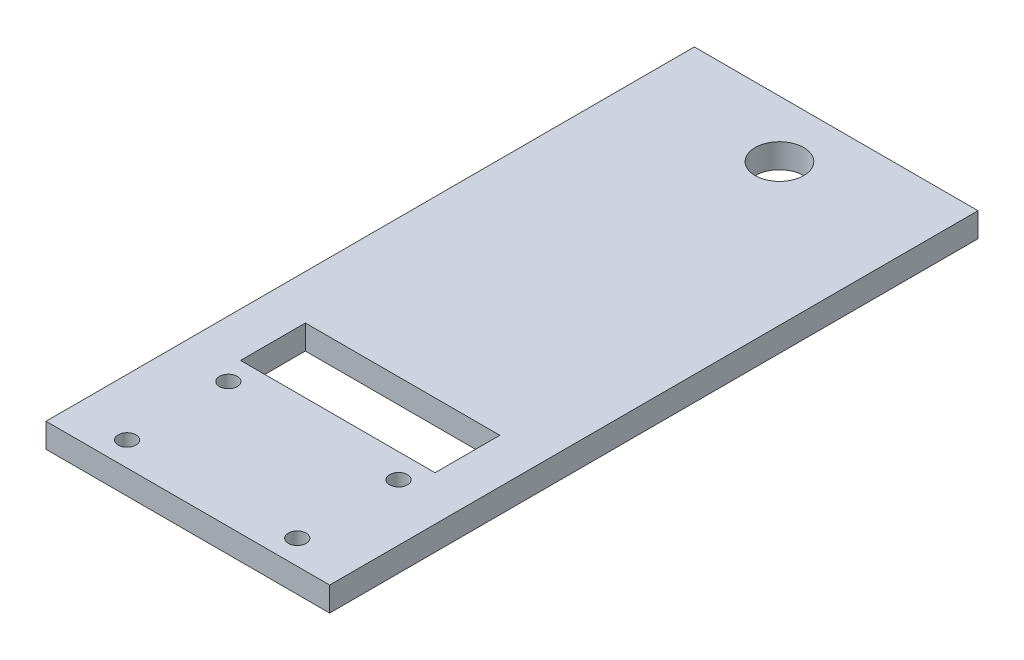
SolidWorks part; units mm, degrees
ref_plane "Front Plane" through (0, 0, 0) normal (0, 0, 1) x (1, 0, 0)
ref_plane "Top Plane" through (0, 0, 0) normal (0, 1, 0) x (1, 0, 0)
ref_plane "Right Plane" through (0, 0, 0) normal (1, 0, 0) x (0, 0, -1)
sketch "Sketch1" plane through (0, 0, 0) normal (0, 1, 0) x (1, 0, 0)
  line L1 (0, 0) -> (35, 0)
  line L2 (0, 0) -> (0, 80)
  line L3 (0, 80) -> (35, 80)
  line L4 (35, 0) -> (35, 80)
  circle A0 centre (7, 3) radius 1.1
  circle A1 centre (28, 3) radius 1.1
  circle A2 centre (7, 15.5) radius 1.1
  circle A3 centre (28, 15.5) radius 1.1
  dimension "D3" = 2.2
  dimension "D4" = 2.2
  dimension "D5" = 2.2
  dimension "D6" = 2.2
  dimension "D7" = 21
  dimension "D8" = 12.5
  dimension "D9" = 12.5
  dimension "D10" = 21
  dimension "D11" = 7
  dimension "D12" = 3
  dimension "D13" = 3
  dimension "D14" = 7
  dimension "D1" = 35
  dimension "D2" = 80
extrude "Boss-Extrude1" add sketch "Sketch1" along normal blind 3
sketch "Sketch2" plane through (0, 0, 0) normal (0, -1, 0) x (1, 0, 0)
  line L2 (35, 0) -> (35, -80) construction
  line L3 (35, -80) -> (0, -80) construction
  circle A0 centre (17.5, -73) radius 3
  dimension "D1" = 6
  dimension "D2" = 17.5
  dimension "D3" = 7
extrude "Cut-Extrude1" cut sketch "Sketch2" against normal through all
sketch "Sketch3" plane through (0, 3, 0) normal (0, 1, 0) x (1, 0, 0)
  line L1 (29.5, 18.5) -> (5.5, 18.5)
  line L2 (29.5, 18.5) -> (29.5, 26.5)
  line L3 (29.5, 26.5) -> (5.5, 26.5)
  line L4 (5.5, 18.5) -> (5.5, 26.5)
  line L5 (35, 0) -> (35, 80) construction
  circle A0 centre (28, 15.5) radius 1.1 construction
  dimension "D1" = 3
  dimension "D2" = 24
  dimension "D3" = 8
  dimension "D4" = 5.5
extrude "Cut-Extrude2" cut sketch "Sketch3" against normal through all
